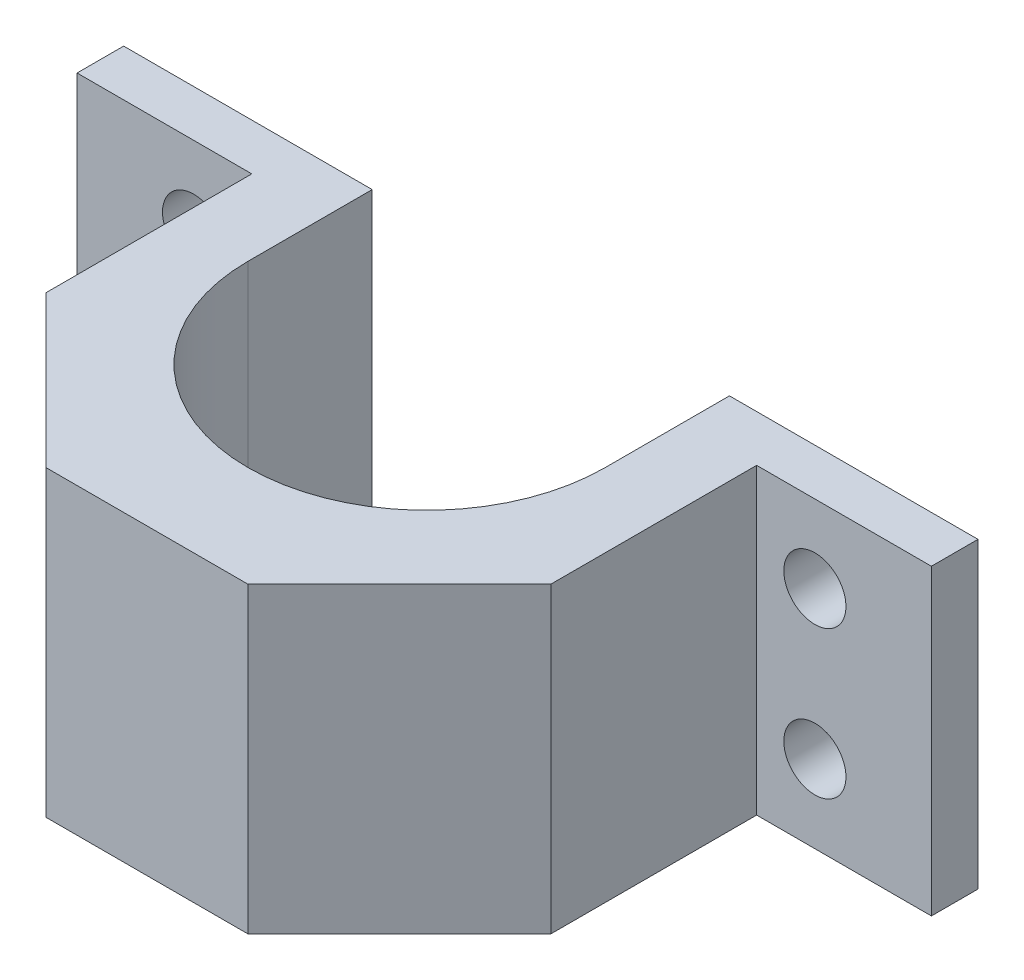
SolidWorks part; units mm, degrees
ref_plane "Front Plane" through (0, 0, 0) normal (0, 0, 1) x (1, 0, 0)
ref_plane "Top Plane" through (0, 0, 0) normal (0, 1, 0) x (1, 0, 0)
ref_plane "Right Plane" through (0, 0, 0) normal (1, 0, 0) x (0, 0, -1)
sketch "Sketch1" plane through (0, 0, 0) normal (0, 1, 0) x (1, 0, 0)
  line L0 (-23, 0) -> (-23, 10)
  line L1 (-55, 16) -> (-23, 16)
  line L2 (-55, 16) -> (-55, 10)
  line L3 (-55, 10) -> (-32.5, 10)
  line L4 (55, 16) -> (55, 10)
  line L7 (23, 0) -> (23, 10)
  line L8 (-13, -36) -> (-32.5, -16.5)
  line L9 (-13, -36) -> (13, -36)
  line L10 (-32.5, -16.5) -> (-32.5, 10)
  line L12 (32.5, -16.5) -> (32.5, 10)
  line L15 (0, -36) -> (0, -23) construction
  line L16 (13, -36) -> (32.5, -16.5)
  line L17 (-23, 10) -> (-23, 16)
  line L18 (23, 10) -> (23, 16)
  line L19 (23, 16) -> (55, 16)
  line L22 (32.5, 10) -> (55, 10)
  arc A2 (-23, 0) -> (23, 0) centre (0, 0) ccw
  point P3 (0, 13)
  point P12 (0, -13)
  dimension "D1" = 65
  dimension "D5" = 23
  dimension "D2" = 6
  dimension "D3" = 16
  dimension "D4" = 52
  dimension "D6" = 110
  dimension "D7" = 26
  dimension "D8" = 45
extrude "Boss-Extrude1" add sketch "Sketch1" along normal blind 39
sketch "Sketch2" plane through (0, 0, -16) normal (0, 0, -1) x (-1, 0, 0)
  line L0 (-55, 19.5) -> (55, 19.5) construction
  line L1 (-55, 39) -> (-55, 0) construction
  line L2 (55, 39) -> (55, 0) construction
  line L3 (55, 19.5) -> (0, 19.5) construction
  line L4 (0, 19.5) -> (0, 0) construction
  line L5 (-23, 0) -> (23, 0) construction
  circle A0 centre (-40, 29) radius 4
  circle A1 centre (-40, 10) radius 4
  circle A2 centre (40, 29) radius 4
  circle A3 centre (40, 10) radius 4
  point P14 (0, 0)
  point P15 (0, 0)
  dimension "D1" = 8
  dimension "D3" = 80
  dimension "D2" = 19
extrude "Cut-Extrude1" cut sketch "Sketch2" against normal through all
